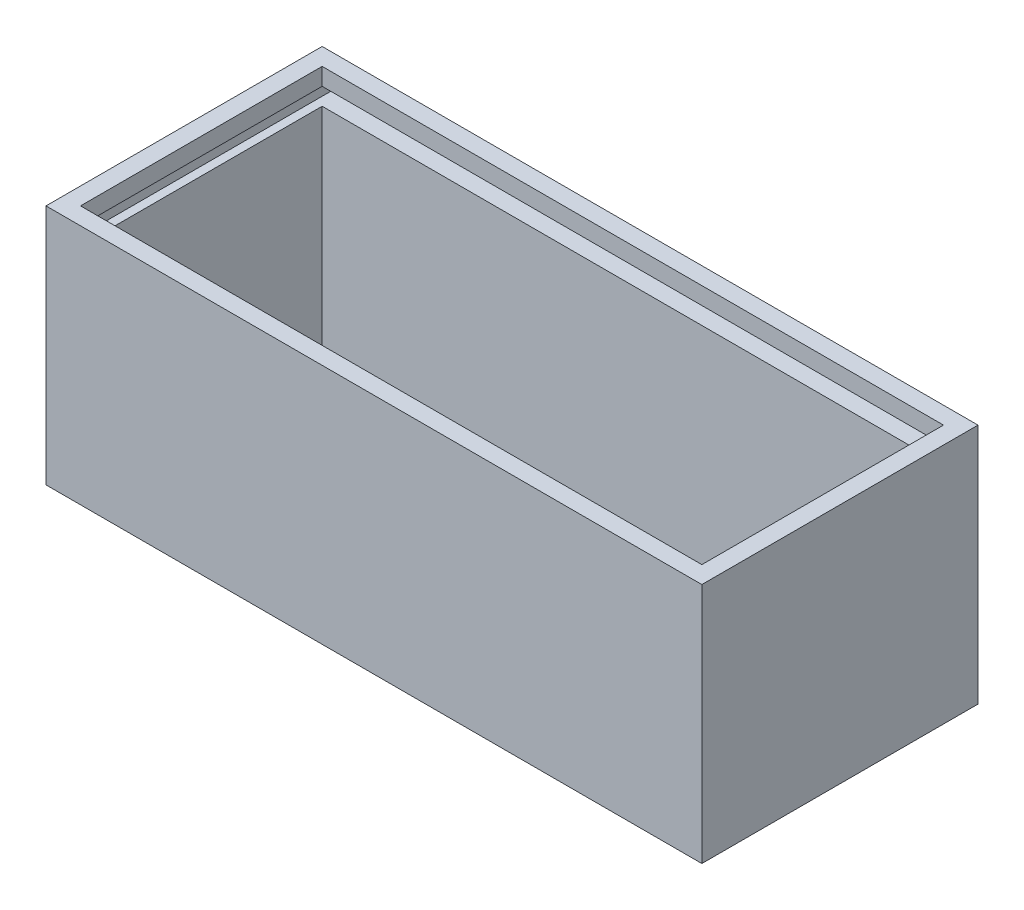
SolidWorks part; units mm, degrees
ref_plane "Front Plane" through (0, 0, 0) normal (0, 0, 1) x (1, 0, 0)
ref_plane "Top Plane" through (0, 0, 0) normal (0, 1, 0) x (1, 0, 0)
ref_plane "Right Plane" through (0, 0, 0) normal (1, 0, 0) x (0, 0, -1)
sketch "Sketch1" plane through (0, 0, 0) normal (0, 1, 0) x (1, 0, 0)
  line L0 (0, 0) -> (190, 0)
  line L1 (0, 0) -> (0, 80)
  line L2 (0, 80) -> (190, 80)
  line L3 (190, 80) -> (190, 0)
  line L4 (0, 80) -> (5, 80)
  line L5 (5, 80) -> (5, 75) construction
  line L6 (95, 80) -> (95, 0) construction
  line L7 (0, 40) -> (190, 40) construction
  line L9 (5, 75) -> (185, 75)
  line L10 (5, 75) -> (5, 5)
  line L11 (5, 5) -> (185, 5)
  line L12 (185, 75) -> (185, 5)
  point P9 (185, 75)
  point P12 (185, 5)
  point P13 (5, 5)
  dimension "D1" = 190
  dimension "D2" = 80
  dimension "D3" = 5
  dimension "D4" = 5
extrude "Boss-Extrude2" add sketch "Sketch1" along normal blind 70 contours L3 L2 L1 L0 L9 L12 L11 L10
sketch "Sketch5" plane through (0, 0, -80) normal (0, 0, -1) x (-1, 0, 0)
  line L0 (-190, 70) -> (-190, 65)
  line L1 (-190, 70) -> (-190, 0) construction
  line L2 (-190, 65) -> (-187.5, 65) construction
  line L3 (0, 70) -> (0, 65)
  line L4 (0, 70) -> (0, 0) construction
  line L5 (0, 65) -> (-2.5, 65) construction
  line L6 (-2.5, 65) -> (-2.5, 60)
  line L7 (-187.5, 65) -> (-187.5, 60)
  line L8 (-187.5, 65) -> (-2.5, 65)
  line L9 (-187.5, 60) -> (-2.5, 60)
  dimension "D1" = 5
  dimension "D2" = 2.5
  dimension "D3" = 5
  dimension "D4" = 2.5
  dimension "D5" = 5
  dimension "D6" = 5
extrude "Cut-Extrude2" cut sketch "Sketch5" against normal blind 75 contours L7 L9 L6 L8
